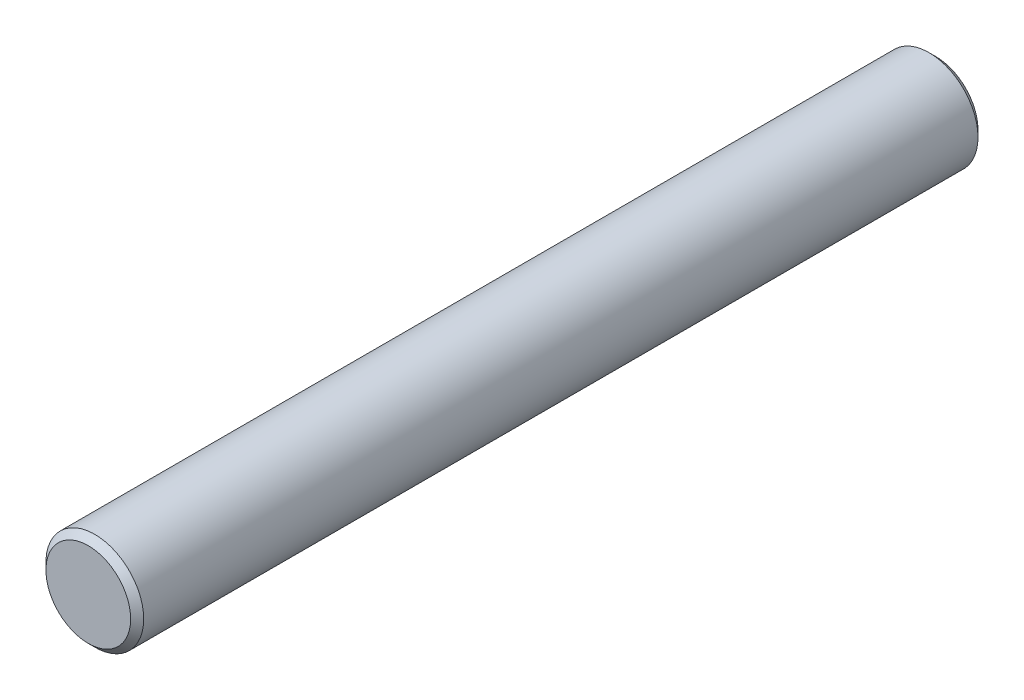
SolidWorks part; units mm, degrees
ref_plane "Front Plane" through (0, 0, 0) normal (0, 0, 1) x (1, 0, 0)
ref_plane "Top Plane" through (0, 0, 0) normal (0, 1, 0) x (1, 0, 0)
ref_plane "Right Plane" through (0, 0, 0) normal (1, 0, 0) x (0, 0, -1)
sketch "Sketch1" plane through (0, 0, 0) normal (0, 0, 1) x (1, 0, 0)
  circle A0 centre (0, 0) radius 0.75
  dimension "D1" = 1.5
extrude "Boss-Extrude1" add sketch "Sketch1" along normal blind 13
chamfer "Chamfer1" distance 0.1 angle 45 2 edges at (0.75, 0, 0) (0.75, 0, 13)
